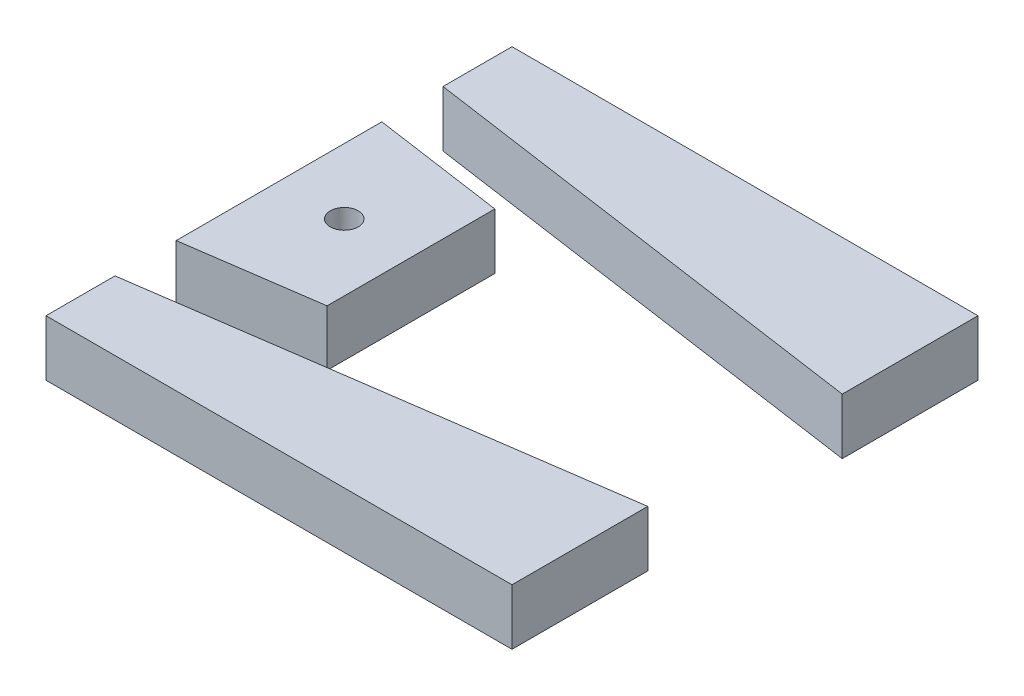
SolidWorks part; units mm, degrees
ref_plane "Front Plane" through (0, 0, 0) normal (0, 0, 1) x (1, 0, 0)
ref_plane "Top Plane" through (0, 0, 0) normal (0, 1, 0) x (1, 0, 0)
ref_plane "Right Plane" through (0, 0, 0) normal (1, 0, 0) x (0, 0, -1)
sketch "Sketch1" plane through (0, 0, 0) normal (0, 1, 0) x (1, 0, 0)
  line L1 (-23.8498, 26.0904) -> (26.1502, 26.0904)
  line L2 (-23.8498, 26.0904) -> (-23.8498, -23.9096)
  line L3 (-23.8498, -23.9096) -> (26.1502, -23.9096)
  line L4 (26.1502, 26.0904) -> (26.1502, -23.9096)
  dimension "D1" = 50
  dimension "D2" = 50
extrude "Boss-Extrude1" add sketch "Sketch1" along normal blind 6
sketch "Sketch2" plane through (0, 6, 0) normal (0, 1, 0) x (1, 0, 0)
  line L0 (-23.8498, -16.5083) -> (26.1502, -9.3421)
  line L1 (-23.8498, 26.0904) -> (-23.8498, -23.9096) construction
  line L2 (26.1502, -23.9096) -> (26.1502, 26.0904) construction
  line L3 (26.1502, -2.7756) -> (-23.8498, -9.9418)
  line L4 (26.1502, 26.0904) -> (-23.8498, 26.0904) construction
  line L5 (-23.8498, 1.0904) -> (41.5814, 1.0904) construction
  line L6 (-23.8498, 18.6891) -> (26.1502, 11.5229)
  line L7 (26.1502, 4.9564) -> (-23.8498, 12.1226)
  line L8 (-23.8498, -9.9418) -> (-23.8498, -16.5083)
  line L9 (26.1502, -9.3421) -> (26.1502, -2.7756)
  line L10 (-23.8498, 12.1226) -> (-23.8498, 18.6891)
  line L11 (-9.6915, -7.9126) -> (-9.6915, 10.0934)
  circle A0 centre (1.1502, 1.0904) radius 10.017 construction
  point P8 (1.1502, 1.0904)
  line M1 (-23.8498, 26.0904) -> (-23.8498, -23.9096)
  line M3 (26.1502, -23.9096) -> (26.1502, 26.0904)
  dimension "D1" = 6.5
  dimension "D2" = 25
  dimension "D3" = 25
extrude "Cut-Extrude1" cut sketch "Sketch2" against normal up to next contours L7 L6 M3 M1 | L3 L0 M3 M1 | L11 L3 L7 M3
hole_wizard "Ø3.0mm Dowel Hole1" positions "Sketch4" profile "Sketch3" hole size "Ø3.0" standard "ANSI Metric" end condition through all
sketch "Sketch4" plane through (0, 6, 0) normal (0, 1, 0) x (1, 0, 0)
  line L0 (-23.8498, 12.1226) -> (-23.8498, -9.9418) construction
  line L4 (-23.8498, -23.9096) -> (26.1502, -23.9096) construction
  point P0 (-16.8498, 1.0904)
  point P10 (-21.1595, -23.9096)
  point P19 (-67.2338, -11.5502)
  dimension "D1" = 7
  dimension "D2" = 25
sketch "Sketch3" plane through (-16.8498, 6, -1.0904) normal (1, 0, 0) x (0, 0, 1)
  line L0 (0, 0) -> (0, 6)
  line L1 (0, 6) -> (1.5, 6)
  line L2 (1.5, 6) -> (1.5, 0)
  line L5 (1.5, 0) -> (0, 0)
  line L11 (0, -6.35) -> (0, 107.95) construction
  dimension "Thru Hole Dia." = 3
  dimension "Thru Hole Depth" = 6
